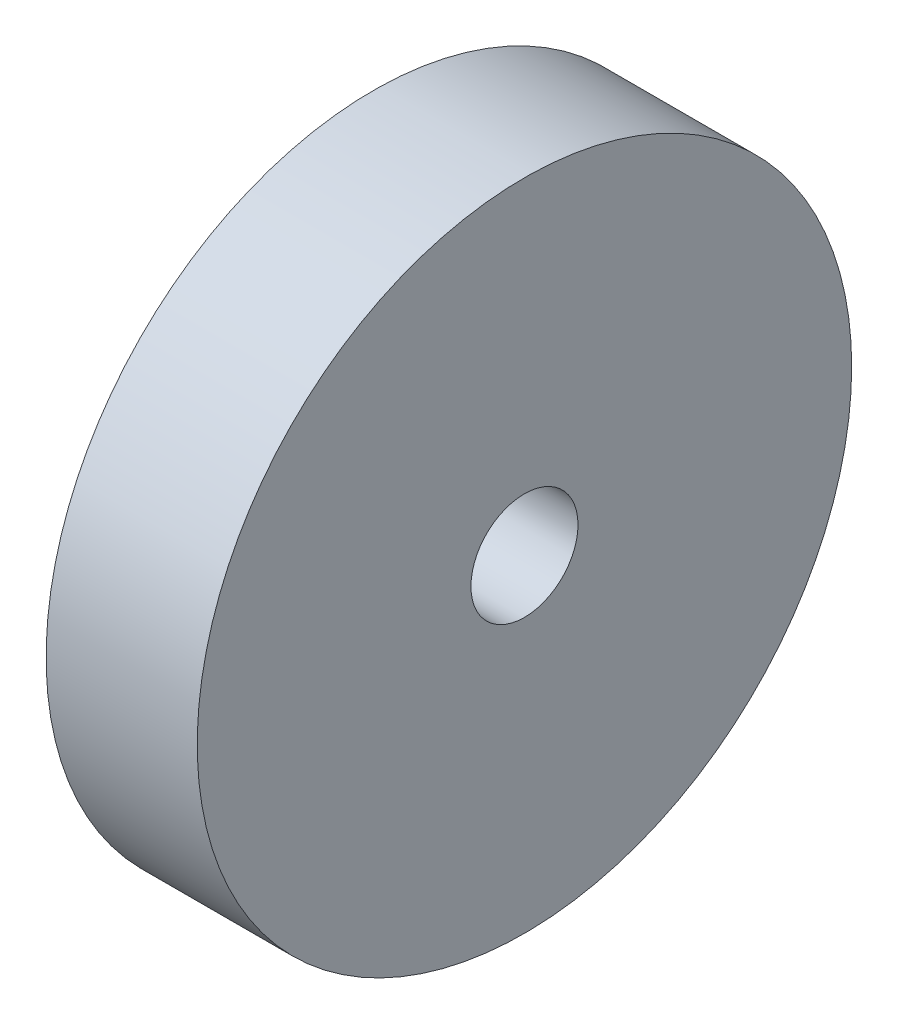
SolidWorks part; units mm, degrees
ref_plane "Front Plane" through (0, 0, 0) normal (0, 0, 1) x (1, 0, 0)
ref_plane "Top Plane" through (0, 0, 0) normal (0, 1, 0) x (1, 0, 0)
ref_plane "Right Plane" through (0, 0, 0) normal (1, 0, 0) x (0, 0, -1)
sketch "Sketch2" plane through (0, 0, 0) normal (1, 0, 0) x (0, 0, -1)
  circle A0 centre (0, 0) radius 11
  dimension "D1" = 22
extrude "Boss-Extrude1" add sketch "Sketch2" along normal blind 5.08
sketch "Sketch3" plane through (0, 0, 0) normal (-1, 0, 0) x (0, 0, 1)
  point P0 (0, 0)
hole_wizard "M3 Clearance Hole1" positions "Sketch4" profile "Sketch5" hole size "M3" standard "ANSI Metric" end condition up to next
sketch "Sketch4" plane through (0, 0, 0) normal (-1, 0, 0) x (0, 0, 1)
  point P0 (0, 0)
sketch "Sketch5" plane through (0, 0, 0) normal (0, 1, 0) x (0, 0, 1)
  line L0 (0, 0) -> (0, 5.08)
  line L1 (0, 5.08) -> (1.8, 5.08)
  line L2 (1.8, 5.08) -> (1.8, 0)
  line L5 (1.8, 0) -> (0, 0)
  line L11 (0, -6.35) -> (0, 107.95) construction
  dimension "Thru Hole Dia." = 3.6
  dimension "Thru Hole Depth" = 5.08
equation "\"MDF\"= 0.2in"
equation "\"D1@Boss-Extrude1\"=\"MDF\""
equation "\"TubeR\"= 0.8in"
equation "\"Foamcore\"= 0.2in"
